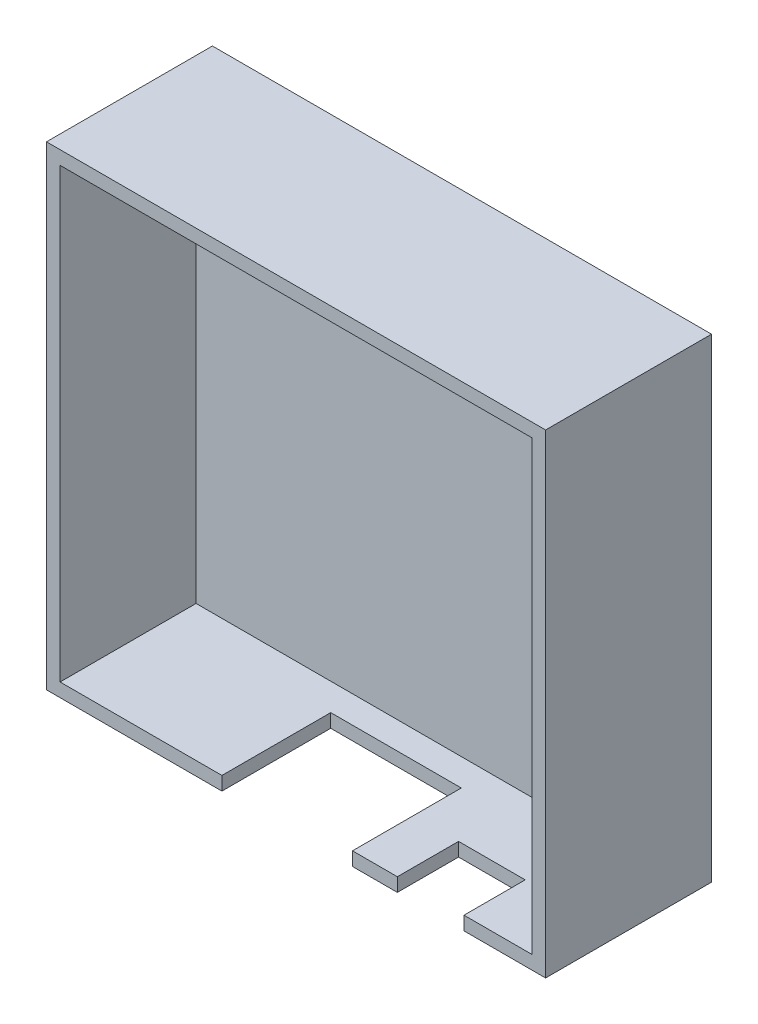
SolidWorks part; units mm, degrees
ref_plane "Front Plane" through (0, 0, 0) normal (0, 0, 1) x (1, 0, 0)
ref_plane "Top Plane" through (0, 0, 0) normal (0, 1, 0) x (1, 0, 0)
ref_plane "Right Plane" through (0, 0, 0) normal (1, 0, 0) x (0, 0, -1)
sketch "Sketch1" plane through (0, 0, 0) normal (0, 0, 1) x (1, 0, 0)
  line L1 (0, 0) -> (36.7, 0)
  line L2 (0, 0) -> (0, 34.9)
  line L3 (0, 34.9) -> (36.7, 34.9)
  line L4 (36.7, 0) -> (36.7, 34.9)
  line L5 (1, 33.9) -> (35.7, 33.9)
  line L6 (1, 33.9) -> (1, 1)
  line L7 (1, 1) -> (35.7, 1)
  line L8 (35.7, 33.9) -> (35.7, 1)
  dimension "D1" = 34.9
  dimension "D2" = 36.7
  dimension "D3" = 1
  dimension "D4" = 1
  dimension "D5" = 1
  dimension "D6" = 1
extrude "Boss-Extrude1" add sketch "Sketch1" along normal blind 8
sketch "Sketch2" plane through (0, 0, 0) normal (0, 0, -1) x (-1, 0, 0)
  line L1 (-36.7, 34.9) -> (0, 34.9)
  line L2 (-36.7, 34.9) -> (-36.7, 0)
  line L3 (-36.7, 0) -> (0, 0)
  line L4 (0, 34.9) -> (0, 0)
extrude "Boss-Extrude2" add sketch "Sketch2" along normal blind 4.2
sketch "Sketch3" plane through (0, 0, 8) normal (0, 0, 1) x (1, 0, 0)
  line L0 (0, 0) -> (36.7, 0) construction
  line L1 (30.7, 0) -> (25.8, 0)
  line L2 (30.7, 0) -> (30.7, 1)
  line L3 (30.7, 1) -> (25.8, 1)
  line L4 (25.8, 0) -> (25.8, 1)
  line L5 (36.7, 0) -> (36.7, 34.9) construction
  line L11 (1, 1) -> (35.7, 1) construction
  dimension "D1" = 6
  dimension "D2" = 4.9
extrude "Cut-Extrude1" cut sketch "Sketch3" against normal offset from surface (4.5 mm away) 3.5 up to face at (18.35, 17.45, 0)
sketch "Sketch4" plane through (0, 0, 8) normal (0, 0, 1) x (1, 0, 0)
  line L0 (0, 0) -> (25.8, 0) construction
  line L1 (22.5, 0) -> (12.9, 0)
  line L2 (22.5, 0) -> (22.5, 1)
  line L3 (22.5, 1) -> (12.9, 1)
  line L4 (12.9, 0) -> (12.9, 1)
  line L5 (1, 1) -> (25.8, 1) construction
  line L6 (25.8, 1) -> (25.8, 0) construction
  dimension "D1" = 3.3
  dimension "D2" = 9.6
extrude "Cut-Extrude2" cut sketch "Sketch4" against normal up to surface (8 mm away) up to face at (18.35, 17.45, 0)
sketch "Sketch5" plane through (0, 0, 0) normal (0, 0, 1) x (1, 0, 0)
  line L0 (1, 33.9) -> (1, 1) construction
  line L1 (35.7, 33.9) -> (1, 33.9)
  line L2 (35.7, 33.9) -> (35.7, 32.4)
  line L3 (35.7, 32.4) -> (1, 32.4)
  line L4 (1, 33.9) -> (1, 32.4)
  dimension "D1" = 1.5
extrude "Boss-Extrude3" add sketch "Sketch5" along normal blind 1.6
sketch "Sketch6" plane through (0, 0, 0) normal (0, 0, 1) x (1, 0, 0)
  line L1 (1, 1) -> (35.7, 1)
  line L2 (1, 1) -> (1, 32.4)
  line L3 (1, 32.4) -> (35.7, 32.4)
  line L4 (35.7, 1) -> (35.7, 32.4)
extrude "Cut-Extrude3" cut sketch "Sketch6" against normal blind 2
